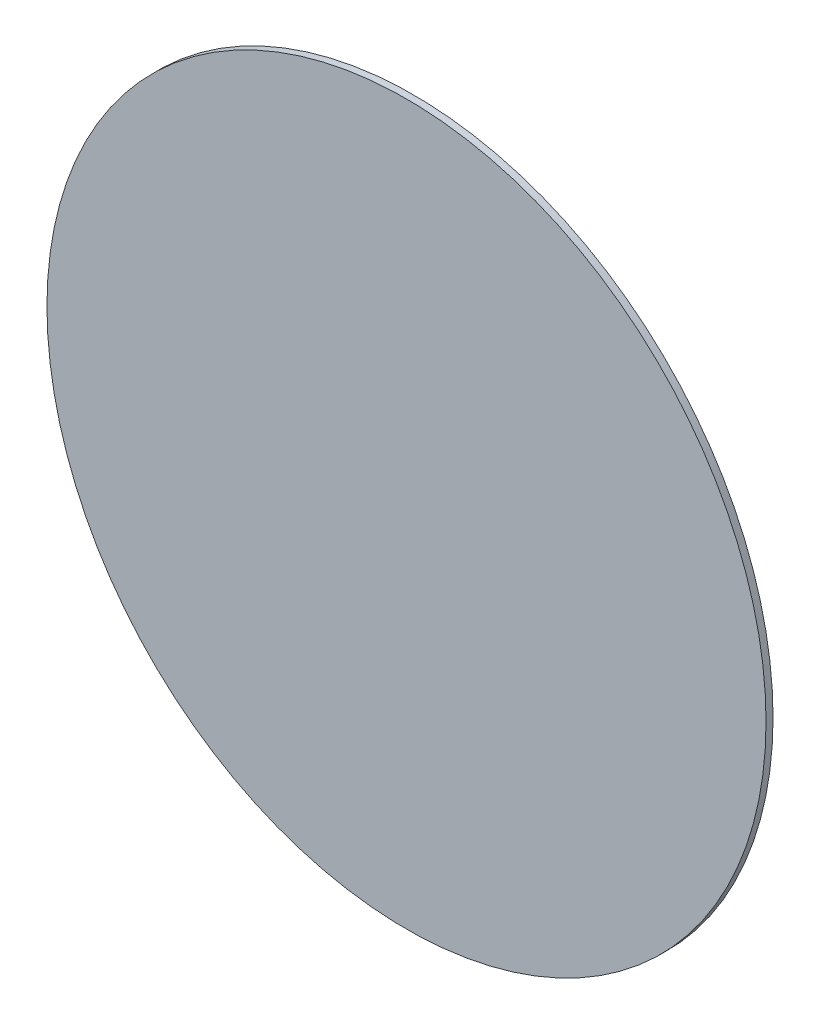
SolidWorks part; units mm, degrees
material "Praseodynium"
ref_plane "Front" through (0, 0, 0) normal (0, 0, 1) x (1, 0, 0)
ref_plane "Top" through (0, 0, 0) normal (0, 1, 0) x (1, 0, 0)
ref_plane "Right" through (0, 0, 0) normal (1, 0, 0) x (0, 0, -1)
sketch "Sketch2" plane through (0, 0, 0) normal (0, 0, 1) x (1, 0, 0)
  circle A0 centre (0, 0) radius 133.5
extrude "Boss-Extrude1" add sketch "Sketch2" along normal blind 2.6
